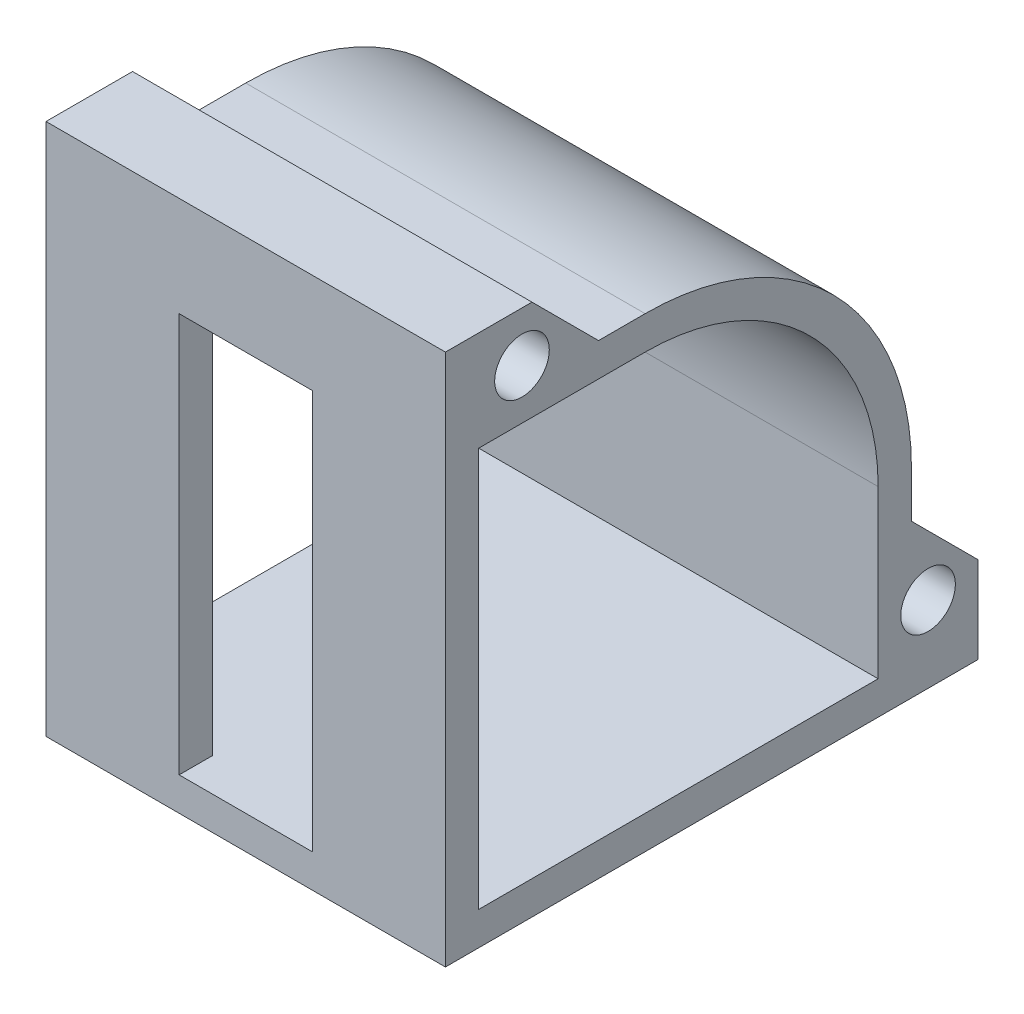
SolidWorks part; units mm, degrees
ref_plane "Спереди" through (0, 0, 0) normal (0, 0, 1) x (1, 0, 0)
ref_plane "Сверху" through (0, 0, 0) normal (0, 1, 0) x (1, 0, 0)
ref_plane "Справа" through (0, 0, 0) normal (1, 0, 0) x (0, 0, -1)
sketch "Sketch2" plane through (0, 0, 0) normal (1, 0, 0) x (0, 0, -1)
  line L0 (0, 40) -> (0, 0) construction
  line L1 (0, 0) -> (40, 0) construction
  line L2 (0, 40) -> (-30, 40)
  line L3 (40, -30) -> (-30, -30)
  line L4 (-25, 35) -> (-25, -25)
  line L5 (40, -30) -> (40, 0)
  line L6 (-30, -30) -> (-30, 40)
  line L7 (-25, -25) -> (35, -25)
  line L8 (35, -25) -> (35, 0)
  line L9 (-25, 35) -> (0, 35)
  line L10 (24.7487, 24.7487) -> (28.2843, 28.2843) construction
  line L12 (-25, 35) -> (-30, 35) construction
  line L13 (-25, -25) -> (-25, -30) construction
  arc A0 (0, 40) -> (40, 0) centre (0, 0) cw
  arc A1 (0, 35) -> (35, 0) centre (0, 0) cw
  dimension "D1" = 40
  dimension "D3" = 5
  dimension "D2" = 70
extrude "Boss-Extrude1" add sketch "Sketch2" along normal blind 60
sketch "Sketch4" plane through (60, 0, 0) normal (1, 0, 0) x (0, 0, -1)
  line L0 (0, 40) -> (-7, 40)
  line L1 (0, 40) -> (-30, 40) construction
  line L2 (-7, 40) -> (-7, 35)
  line L3 (0, 35) -> (-25, 35) construction
  line L4 (-7, 35) -> (0, 35)
  line L5 (35, -7) -> (40, -7)
  line L6 (35, -25) -> (35, 0) construction
  line L7 (40, -30) -> (40, 0) construction
  line L8 (40, -7) -> (40, 0)
  line L9 (35, 0) -> (35, -7)
  arc A0 (0, 40) -> (40, 0) centre (0, 0) cw
  arc A1 (35, 0) -> (0, 35) centre (0, 0) ccw
  arc A3 (40, 0) -> (0, 40) centre (0, 0) ccw construction
  dimension "D1" = 7
  dimension "D2" = 7
extrude "Cut-Extrude1" cut sketch "Sketch4" against normal blind 7
sketch "Sketch5" plane through (0, 0, 30) normal (0, 0, 1) x (1, 0, 0)
  line L0 (30, 40) -> (30, -30) construction
  line L1 (60, 40) -> (0, 40) construction
  line L2 (60, -30) -> (0, -30) construction
  line L4 (40, -25) -> (20, -25)
  line L5 (40, -25) -> (40, 35)
  line L6 (40, 35) -> (20, 35)
  line L7 (20, -25) -> (20, 35)
  line L8 (40, -25) -> (20, 35) construction
  line L9 (40, 35) -> (20, -25) construction
  point P6 (30, 5)
  dimension "D1" = 20
  dimension "D2" = 60
extrude "Cut-Extrude2" cut sketch "Sketch5" against normal up to next
sketch "Sketch6" plane through (60, 0, 0) normal (1, 0, 0) x (0, 0, -1)
  line L0 (-7, 40) -> (-30, 40)
  line L1 (40, -7) -> (40, -30)
  line L2 (-30, 40) -> (-30, 50)
  line L3 (-30, 50) -> (-7, 50)
  line L4 (-7, 50) -> (-7, 40)
  line L5 (40, -7) -> (50, -7)
  line L6 (50, -7) -> (50, -30)
  line L7 (50, -30) -> (40, -30)
  dimension "D1" = 10
extrude "Boss-Extrude3" add sketch "Sketch6" against normal up to surface (60 mm away) up to face at (0, 5.6569, -5.6569)
sketch "Sketch8" plane through (60, 0, 0) normal (1, 0, 0) x (0, 0, -1)
  line L0 (-30, 42.5) -> (-7, 42.5) construction
  line L1 (-30, 50) -> (-30, -30) construction
  line L2 (-7, 50) -> (-7, 35) construction
  line L3 (42.5, -7) -> (42.5, -30) construction
  line L4 (35, -7) -> (50, -7) construction
  line L5 (-30, -30) -> (50, -30) construction
  circle A0 centre (-18.5, 42.5) radius 4.1
  circle A1 centre (42.5, -18.5) radius 4.1
  point P16 (-7, 42.5)
  dimension "D1" = 8.2
extrude "Cut-Extrude3" cut sketch "Sketch8" against normal through all
chamfer "Chamfer2" distance 10 angle 45 2 edges at (30, -7, -50) (30, 50, 7)
sketch "Sketch9" plane through (53, 0, 0) normal (1, 0, 0) x (0, 0, -1)
  line L0 (0, 40) -> (-7, 40)
  line L1 (-7, 40) -> (-7, 35)
  line L2 (-7, 35) -> (0, 35)
  line L3 (35, 0) -> (35, -7)
  line L4 (35, -7) -> (40, -7)
  line L5 (40, -7) -> (40, 0)
  arc A0 (0, 35) -> (35, 0) centre (0, 0) cw
  arc A1 (35, 0) -> (0, 35) centre (0, 0) ccw construction
  arc A2 (0, 40) -> (40, 0) centre (0, 0) cw
  arc A3 (40, 0) -> (0, 40) centre (0, 0) ccw construction
extrude "Boss-Extrude4" add sketch "Sketch9" along normal up to surface (7 mm away) up to face at (60, -18.5, -46.6)
sketch "Sketch10" plane through (0, 0, 0) normal (-1, 0, 0) x (0, 0, 1)
  line L0 (7, 40) -> (-13, 40)
  line L1 (-70, -10) -> (-70, -30)
  line L2 (-70, -30) -> (30, -30)
  line L3 (30, 50) -> (30, -30) construction
  line L4 (30, -30) -> (30, 50)
  line L5 (30, 50) -> (17, 50)
  line L6 (30, -30) -> (-50, -30) construction
  line L7 (17, 50) -> (7, 40)
  line L8 (-13, 40) -> (-70, -10)
  line L9 (18.5, 42.5) -> (30, -30) construction
  line L10 (30, 42.5) -> (18.5, 42.5) construction
  line L11 (-42.5, -18.5) -> (-42.5, -30) construction
  line L12 (-42.5, -18.5) -> (-70, -30) construction
  line L13 (-50, -30) -> (-42.5, -30) construction
  dimension "D1" = 100
  dimension "D2" = 20
  dimension "D3" = 20
  dimension "D4" = 131.257
  dimension "D5" = 13
  dimension "D6" = 80
  dimension "D7" = 14.1421
  dimension "D8" = 11.5
  dimension "D9" = 72.5
  dimension "D10" = 11.5
  dimension "D11" = 27.5
